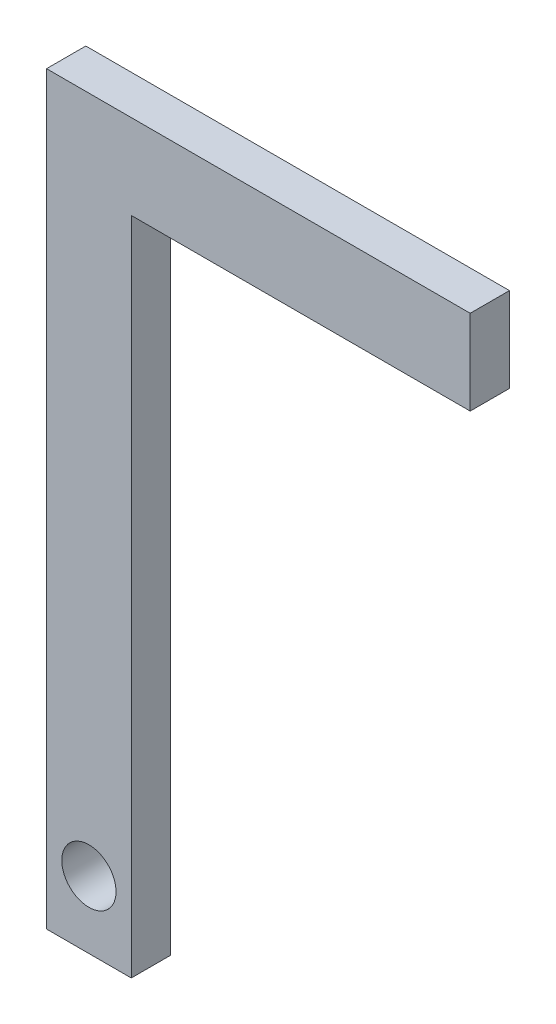
SolidWorks part; units mm, degrees
ref_plane "前视基准面" through (0, 0, 0) normal (0, 0, 1) x (1, 0, 0)
ref_plane "上视基准面" through (0, 0, 0) normal (0, 1, 0) x (1, 0, 0)
ref_plane "右视基准面" through (0, 0, 0) normal (1, 0, 0) x (0, 0, -1)
sketch "草图3" plane through (0, 0, 0) normal (0, 0, 1) x (1, 0, 0)
  line L0 (-3.7818, 65.9564) -> (-3.7818, -67.4627) construction
  line L1 (-11.2818, 65.9564) -> (3.7182, 65.9564)
  line L2 (-11.2818, 65.9564) -> (-11.2818, -65.9564)
  line L3 (-11.2818, -65.9564) -> (3.7182, -65.9564)
  line L4 (3.7182, 65.9564) -> (3.7182, -65.9564)
  line L5 (3.7182, 65.9564) -> (93.7182, 65.9564)
  line L7 (3.7182, 50.9564) -> (93.7182, 50.9564)
  line L8 (93.7182, 65.9564) -> (93.7182, 50.9564)
  dimension "D1" = 15
  dimension "D2" = 90
  dimension "D3" = 15
extrude "凸台-拉伸2" add sketch "草图3" along normal blind 6.95 contours L1 L2 L3 L4
sketch "草图4" plane through (0, 0, 0) normal (0, 0, 1) x (1, 0, 0)
  line L1 (3.7182, 65.9564) -> (63.7182, 65.9564)
  line L2 (3.7182, 65.9564) -> (3.7182, 50.9564)
  line L3 (3.7182, 50.9564) -> (63.7182, 50.9564)
  line L4 (63.7182, 65.9564) -> (63.7182, 50.9564)
  dimension "D1" = 15
  dimension "D2" = 60
extrude "凸台-拉伸3" add sketch "草图4" along normal blind 6.95
sketch "草图5" plane through (0, 0, 0) normal (0, 0, 1) x (1, 0, 0)
  line L0 (-3.7818, -65.9564) -> (-3.7818, 65.9564) construction
  line L1 (-11.2818, -65.9564) -> (3.7182, -65.9564) construction
  line L2 (-11.2818, 65.9564) -> (63.7182, 65.9564) construction
  circle A0 centre (-3.7818, -54.073) radius 4.8
extrude "切除-拉伸5" cut sketch "草图5" along normal through all contours A0
